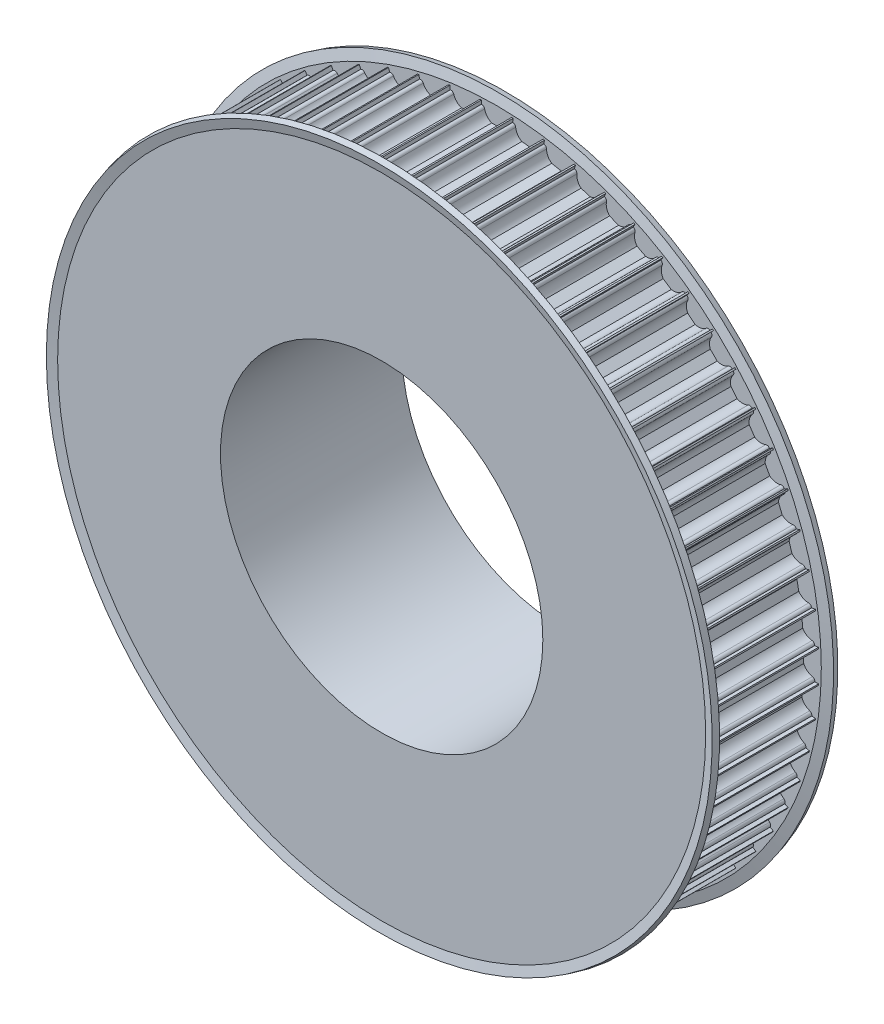
SolidWorks part; units mm, degrees
ref_plane "Front Plane" through (0, 0, 0) normal (0, 0, 1) x (1, 0, 0)
ref_plane "Top Plane" through (0, 0, 0) normal (0, 1, 0) x (1, 0, 0)
ref_plane "Right Plane" through (0, 0, 0) normal (1, 0, 0) x (0, 0, -1)
sketch "Sketch1" plane through (0, 0, 0) normal (1, 0, 0) x (0, 0, -1)
  line L0 (0, 0) -> (25.0004, 0) construction
  line L1 (0, 40) -> (0, 80)
  line L2 (0, 80) -> (30, 80)
  line L3 (30, 80) -> (30, 55.5)
  line L4 (30, 55.5) -> (45, 55.5)
  line L5 (45, 55.5) -> (45, 40)
  line L6 (0, 40) -> (45, 40)
  dimension "D1" = 40
  dimension "D2" = 80
  dimension "D3" = 30
  dimension "D4" = 15
  dimension "D5" = 15.5
revolve "Revolve1" add sketch "Sketch1" angle 360 about L0
sketch "Sketch2" plane through (0, 0, 0) normal (0, 0, 1) x (1, 0, 0)
  line L0 (-3.6742, 79) -> (-3.75, 79)
  line L1 (-3.75, 79) -> (-3.75, 81)
  line L2 (-3.75, 81) -> (3.75, 81)
  line L3 (3.75, 81) -> (3.75, 79)
  line L4 (3.6742, 79) -> (3.75, 79)
  line L5 (-1.199, 76.25) -> (1.199, 76.25)
  arc A0 (2.9394, 78.4) -> (1.199, 76.25) centre (0, 79) cw
  arc A1 (3.6742, 79) -> (2.9394, 78.4) centre (3.6742, 78.25) ccw
  arc A2 (-2.9394, 78.4) -> (-3.6742, 79) centre (-3.6742, 78.25) ccw
  arc A3 (-1.199, 76.25) -> (-2.9394, 78.4) centre (0, 79) cw
  point P9 (3, 79)
  point P12 (-3, 79)
  dimension "D1" = 3
  dimension "D5" = 0.75
  dimension "D2" = 79
  dimension "D3" = 7.5
  dimension "D4" = 2
  dimension "D6" = 2.75
extrude "Cut-Extrude1" cut sketch "Sketch2" against normal up to next (30 mm away)
pattern_circular "CirPattern2" count 64 over 360 about axis through (0, 0, 0) along (0, 0, 1) of "Cut-Extrude1"
sketch "Sketch3" plane through (0, 0, 0) normal (1, 0, 0) x (0, 0, -1)
  line L0 (15, -40.9775) -> (15, 34.0456) construction
  line L1 (30, -40.9775) -> (0, -40.9775) construction
  line L2 (0, 34.0456) -> (30, 34.0456) construction
  line L3 (30, 55.5) -> (30, 80.4125)
  line L4 (30, 80.4125) -> (30.592, 82.6218)
  line L5 (30.592, 82.6218) -> (29.1431, 83.01)
  line L6 (29.1431, 83.01) -> (28.5, 80.61)
  line L7 (28.5, 80.61) -> (28.5, 55.5)
  line L8 (28.5, 55.5) -> (30, 55.5)
  line L9 (0, 80.4125) -> (-0.592, 82.6218)
  line L10 (-0.592, 82.6218) -> (0.8569, 83.01)
  line L11 (0.8569, 83.01) -> (1.5, 80.61)
  line L12 (1.5, 80.61) -> (1.5, 55.5)
  line L13 (1.5, 55.5) -> (0, 55.5)
  line L14 (0, 55.5) -> (0, 80.4125)
  line L15 (0, 0) -> (-18.4442, 0) construction
  dimension "D1" = 15
  dimension "D2" = 25.11
  dimension "D3" = 2.4
  dimension "D4" = 1.5
revolve "Revolve2" add sketch "Sketch3" angle 360 about L15
